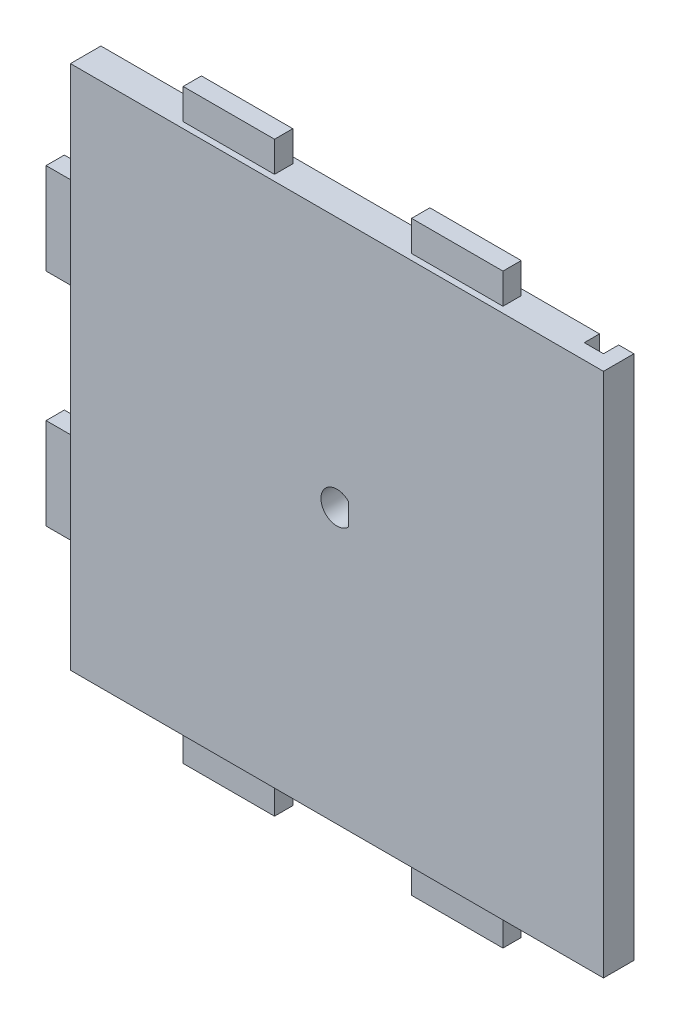
SolidWorks part; units mm, degrees
material "ABS"
ref_plane "Plano frontal" through (0, 0, 0) normal (0, 0, 1) x (1, 0, 0)
ref_plane "Plano superior" through (0, 0, 0) normal (0, 1, 0) x (1, 0, 0)
ref_plane "Plano direito" through (0, 0, 0) normal (1, 0, 0) x (0, 0, -1)
sketch "Esboço1" plane through (0, 0, 0) normal (0, 0, 1) x (1, 0, 0)
  line L1 (87.5, -86.25) -> (-87.5, -86.25)
  line L2 (87.5, -86.25) -> (87.5, 86.25)
  line L3 (87.5, 86.25) -> (-87.5, 86.25)
  line L4 (-87.5, -86.25) -> (-87.5, 86.25)
  line L5 (87.5, -86.25) -> (-87.5, 86.25) construction
  line L6 (87.5, 86.25) -> (-87.5, -86.25) construction
  point P0 (0, 0)
  dimension "D1" = 172.5
  dimension "D2" = 175
extrude "Ressalto-extrusão1" add sketch "Esboço1" along normal blind 10
sketch "Esboço5" plane through (0, 86.25, 0) normal (0, 1, 0) x (1, 0, 0)
  line L0 (0, 0) -> (0, -10) construction
  line L1 (87.5, -10) -> (-87.5, -10) construction
  line L2 (-87.5, -5) -> (87.5, -5) construction
  line L3 (-87.5, -10) -> (-87.5, 0) construction
  line L4 (87.5, -10) -> (87.5, 0) construction
  line L5 (22.5, -2) -> (52.5, -8) construction
  line L6 (-22.5, -8) -> (-52.5, -8)
  line L7 (-22.5, -8) -> (-22.5, -2)
  line L8 (-22.5, -2) -> (-52.5, -2)
  line L9 (-52.5, -8) -> (-52.5, -2)
  line L10 (-22.5, -8) -> (-52.5, -2) construction
  line L11 (-22.5, -2) -> (-52.5, -8) construction
  line L12 (22.5, -8) -> (52.5, -2) construction
  line L13 (52.5, -8) -> (52.5, -2)
  line L14 (22.5, -2) -> (52.5, -2)
  line L15 (22.5, -8) -> (22.5, -2)
  line L16 (22.5, -8) -> (52.5, -8)
  point P11 (-37.5, -5)
  point P20 (37.5, -5)
  dimension "D1" = 30
  dimension "D2" = 6
  dimension "D3" = 50
extrude "Ressalto-extrusão5" add sketch "Esboço5" along normal blind 10
sketch "Esboço6" plane through (-87.5, 0, 0) normal (-1, 0, 0) x (0, 0, 1)
  line L0 (5, 80.8371) -> (5, -100.2795) construction
  line L1 (0, 86.25) -> (0, -86.25) construction
  line L2 (-31.1105, 0) -> (49.0505, 0) construction
  line L3 (10, 86.25) -> (0, 86.25) construction
  line L4 (8, 21.25) -> (2, 21.25)
  line L5 (8, 21.25) -> (8, 51.25)
  line L6 (8, 51.25) -> (2, 51.25)
  line L7 (2, 21.25) -> (2, 51.25)
  line L8 (8, 21.25) -> (2, 51.25) construction
  line L9 (8, 51.25) -> (2, 21.25) construction
  line L10 (8, -51.25) -> (2, -21.25) construction
  line L11 (8, -21.25) -> (2, -51.25) construction
  line L12 (2, -21.25) -> (2, -51.25)
  line L13 (8, -51.25) -> (2, -51.25)
  line L14 (8, -21.25) -> (8, -51.25)
  line L15 (8, -21.25) -> (2, -21.25)
  point P6 (5, 36.25)
  point P19 (5, -36.25)
  dimension "D1" = 5
  dimension "D2" = 6
  dimension "D3" = 30
  dimension "D4" = 50
extrude "Ressalto-extrusão6" add sketch "Esboço6" along normal blind 10
sketch "Esboço7" plane through (0, -86.25, 0) normal (0, -1, 0) x (1, 0, 0)
  line L0 (-118.1326, 5) -> (111.1308, 5) construction
  line L1 (-87.5, 10) -> (87.5, 10) construction
  line L2 (0, -18.9857) -> (0, 24.411) construction
  line L3 (-87.5, 10) -> (-87.5, 0) construction
  line L4 (-22.5, 2) -> (-52.5, 2)
  line L5 (-22.5, 2) -> (-22.5, 8)
  line L6 (-22.5, 8) -> (-52.5, 8)
  line L7 (-52.5, 2) -> (-52.5, 8)
  line L8 (-22.5, 2) -> (-52.5, 8) construction
  line L9 (-22.5, 8) -> (-52.5, 2) construction
  line L10 (22.5, 8) -> (52.5, 2) construction
  line L11 (22.5, 2) -> (52.5, 8) construction
  line L12 (52.5, 2) -> (52.5, 8)
  line L13 (22.5, 8) -> (52.5, 8)
  line L14 (22.5, 2) -> (22.5, 8)
  line L15 (22.5, 2) -> (52.5, 2)
  point P6 (-37.5, 5)
  point P19 (37.5, 5)
  dimension "D1" = 5
  dimension "D2" = 30
  dimension "D3" = 6
  dimension "D4" = 50
extrude "Ressalto-extrusão7" add sketch "Esboço7" along normal blind 10
sketch "Esboço8" plane through (0, 0, 0) normal (0, 0, -1) x (-1, 0, 0)
  line L0 (-117.868, 0) -> (123.9992, 0) construction
  line L1 (-87.5, 86.25) -> (87.5, 86.25) construction
  line L2 (-76.2, -86.25) -> (-82.5, -86.25)
  line L3 (-76.2, -86.25) -> (-76.2, 86.25)
  line L4 (-76.2, 86.25) -> (-82.5, 86.25)
  line L5 (-82.5, -86.25) -> (-82.5, 86.25)
  line L6 (-76.2, -86.25) -> (-82.5, 86.25) construction
  line L7 (-76.2, 86.25) -> (-82.5, -86.25) construction
  line L8 (-87.5, -86.25) -> (-87.5, 86.25) construction
  point P2 (-79.35, 0)
  dimension "D1" = 5
  dimension "D2" = 6.3
extrude "Corte-extrusão1" cut sketch "Esboço8" against normal blind 5
sketch "Esboço9" plane through (-87.5, 0, 0) normal (-1, 0, 0) x (0, 0, 1)
  line L0 (5, 94.9914) -> (5, -96.7804) construction
  line L1 (0, 86.25) -> (0, -86.25) construction
  line L2 (10, -86.25) -> (0, -86.25) construction
  line L3 (-27.2326, 0) -> (31.072, 0) construction
  circle A1 centre (5, -71.25) radius 1.5
  dimension "D2" = 3
  dimension "D3" = 15
  dimension "D1" = 5
extrude "Corte-extrusão2" cut sketch "Esboço9" against normal blind 8
sketch "Esboço10" plane through (0, -86.25, 0) normal (0, -1, 0) x (1, 0, 0)
  line L0 (-109.7376, 5) -> (105.812, 5) construction
  line L1 (-87.5, 10) -> (87.5, 10) construction
  line L2 (87.5, 10) -> (87.5, 0) construction
  circle A0 centre (65, 5) radius 1.5
  dimension "D2" = 3
  dimension "D3" = 22.5
  dimension "D1" = 5
extrude "Corte-extrusão3" cut sketch "Esboço10" against normal blind 8
sketch "Esboço11" plane through (0, 0, 10) normal (0, 0, 1) x (1, 0, 0)
  line L0 (-102.0342, 3.75) -> (100.973, 3.75) construction
  line L1 (87.5, 86.25) -> (-87.5, 86.25) construction
  line L2 (0, 94.9914) -> (0, -102.1472) construction
  line L4 (6.65, -1.25) -> (3.85, -1.25)
  line L5 (6.65, -1.25) -> (6.65, 8.75)
  line L6 (6.65, 8.75) -> (3.85, 8.75)
  line L7 (3.85, -1.25) -> (3.85, 8.75)
  line L8 (6.65, -1.25) -> (3.85, 8.75) construction
  line L9 (6.65, 8.75) -> (3.85, -1.25) construction
  circle A0 centre (0, 3.75) radius 5.25
  point P11 (5.25, 3.75)
  dimension "D2" = 10.5
  dimension "D1" = 82.5
  dimension "D3" = 10
  dimension "D4" = 2.8
extrude "Corte-extrusão4" cut sketch "Esboço11" against normal through all contours L7 A0
